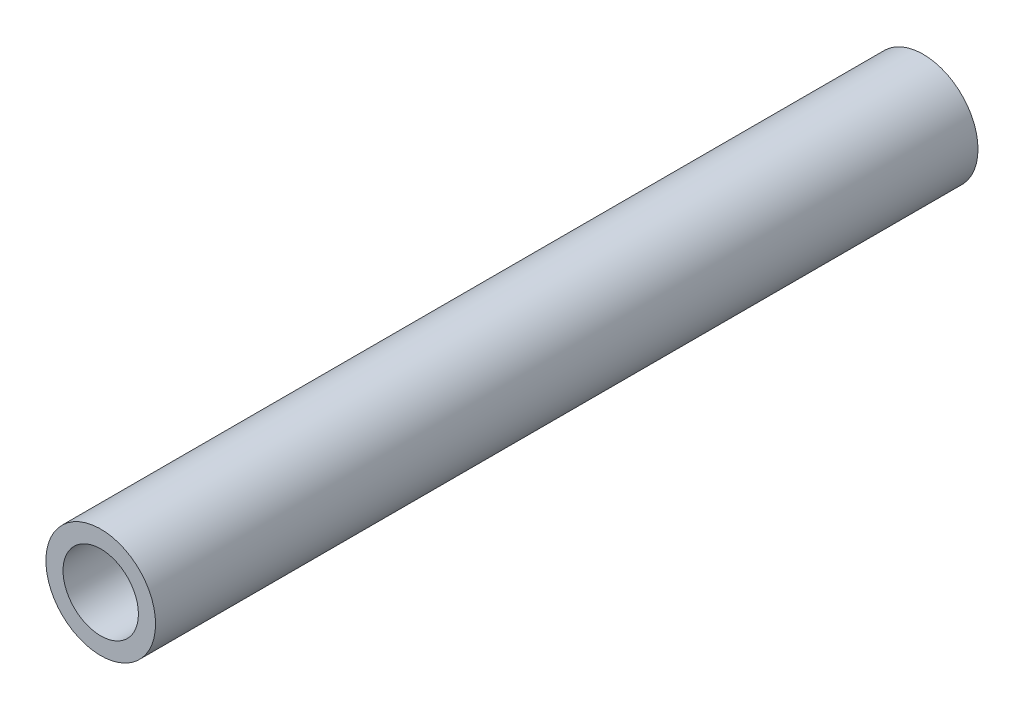
SolidWorks part; units mm, degrees
material "Cast Carbon Steel"
ref_plane "Front Plane" through (0, 0, 0) normal (0, 0, 1) x (1, 0, 0)
ref_plane "Top Plane" through (0, 0, 0) normal (0, 1, 0) x (1, 0, 0)
ref_plane "Right Plane" through (0, 0, 0) normal (1, 0, 0) x (0, 0, -1)
sketch "Sketch1" plane through (0, 0, 0) normal (0, 0, 1) x (1, 0, 0)
  circle A0 centre (0, 0) radius 12.7
  circle A1 centre (0, 0) radius 8.7312
  dimension "D1" = 25.4
  dimension "D2" = 17.4625
extrude "Boss-Extrude1" add sketch "Sketch1" along normal blind 190.5
